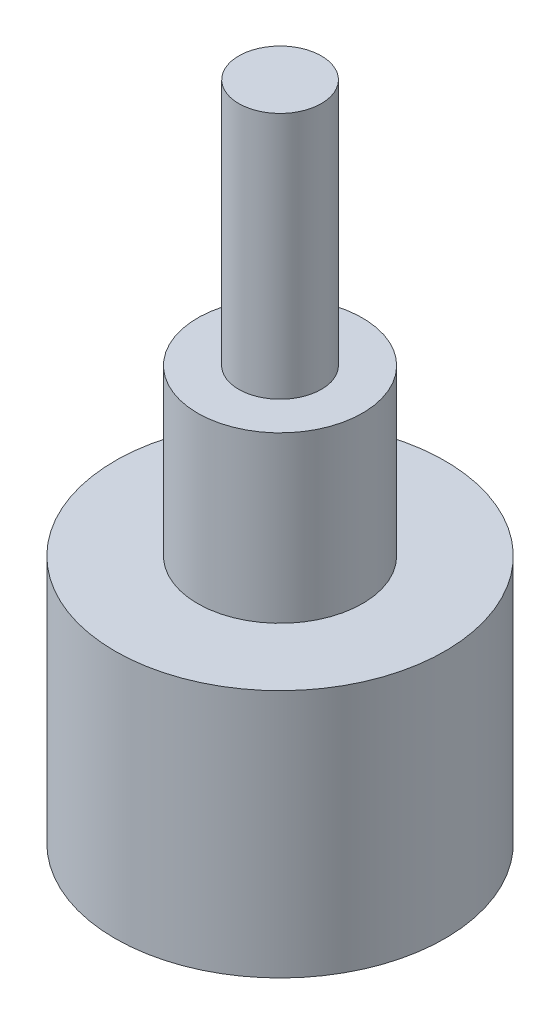
SolidWorks part; units mm, degrees
ref_plane "Front Plane" through (0, 0, 0) normal (0, 0, 1) x (1, 0, 0)
ref_plane "Top Plane" through (0, 0, 0) normal (0, 1, 0) x (1, 0, 0)
ref_plane "Right Plane" through (0, 0, 0) normal (1, 0, 0) x (0, 0, -1)
sketch "Sketch1" plane through (0, 0, 0) normal (0, 1, 0) x (1, 0, 0)
  circle A0 centre (0, 0) radius 6.35
extrude "Boss-Extrude1" add sketch "Sketch1" along normal blind 9.58
sketch "Sketch4" plane through (0, 9.58, 0) normal (0, 1, 0) x (1, 0, 0)
  circle A0 centre (0, 0) radius 3.175
extrude "Boss-Extrude2" add sketch "Sketch4" along normal blind 6.35
sketch "Sketch5" plane through (0, 15.93, 0) normal (0, 1, 0) x (1, 0, 0)
  circle A0 centre (0, 0) radius 1.59
extrude "Boss-Extrude3" add sketch "Sketch5" along normal blind 9.53
